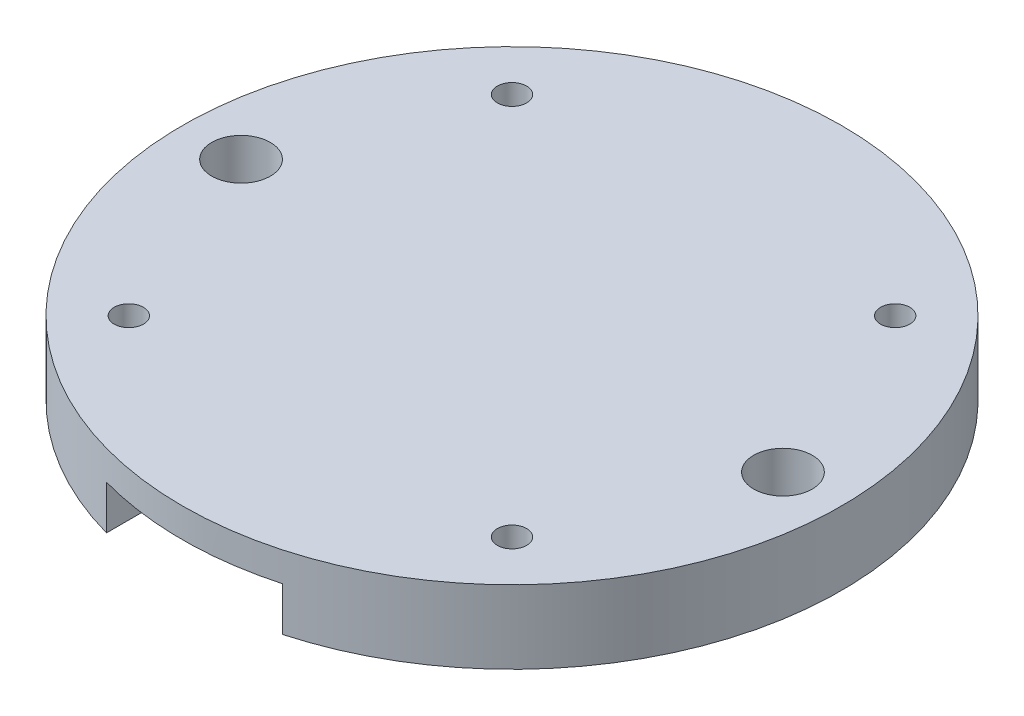
SolidWorks part; units mm, degrees
ref_plane "前视基准面" through (0, 0, 0) normal (0, 0, 1) x (1, 0, 0)
ref_plane "上视基准面" through (0, 0, 0) normal (0, 1, 0) x (1, 0, 0)
ref_plane "右视基准面" through (0, 0, 0) normal (1, 0, 0) x (0, 0, -1)
sketch "草图1" plane through (0, 0, 0) normal (0, 1, 0) x (1, 0, 0)
  line L0 (0, 0) -> (39.3428, 0) construction
  line L1 (0, 0) -> (0, 31.7187) construction
  circle A0 centre (0, 0) radius 22.5
  circle A1 centre (18.5, 0) radius 2
  circle A2 centre (-18.5, 0) radius 2
  dimension "D1" = 45
  dimension "D2" = 4
  dimension "D3" = 18.5
extrude "凸台-拉伸1" add sketch "草图1" along normal blind 5
sketch "草图2" plane through (0, 0, 0) normal (0, 1, 0) x (1, 0, 0)
  circle A0 centre (0, 0) radius 10.25
  dimension "D1" = 20.5
extrude "切除-拉伸1" cut sketch "草图2" along normal blind 1
sketch "草图3" plane through (0, 0, 0) normal (0, 0, 1) x (1, 0, 0)
  line L0 (6, 0) -> (-6, 0)
  line L1 (-6, 0) -> (-6, 3)
  line L2 (-6, 3) -> (6, 3)
  line L3 (0, 14.0479) -> (0, -9.6469) construction
  line L4 (6, 0) -> (6, 3)
  point P8 (0, 0)
  point P9 (0, 3)
  dimension "D1" = 12
  dimension "D2" = 3
extrude "切除-拉伸2" cut sketch "草图3" against normal through all both and the other way through all
sketch "草图4" plane through (0, 5, 0) normal (0, 1, 0) x (1, 0, 0)
  line L0 (0, 0) -> (31.0084, 0) construction
  line L1 (0, 0) -> (0, 24.9359) construction
  line L2 (0, 0) -> (21.3398, 21.3398) construction
  circle A0 centre (13.0815, 13.0815) radius 1
  circle A1 centre (13.0815, -13.0815) radius 1
  circle A2 centre (-13.0815, 13.0815) radius 1
  circle A3 centre (-13.0815, -13.0815) radius 1
  dimension "D1" = 2
  dimension "D2" = 18.5
  dimension "D3" = 45
extrude "切除-拉伸3" cut sketch "草图4" against normal through all
